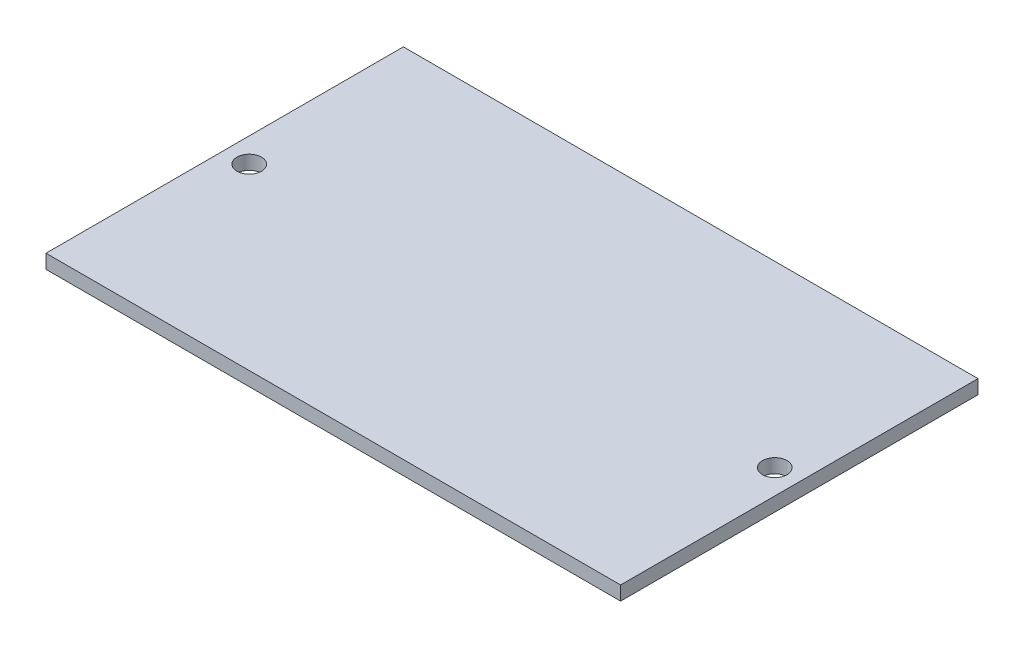
SolidWorks part; units mm, degrees
ref_plane "Front Plane" through (0, 0, 0) normal (0, 0, 1) x (1, 0, 0)
ref_plane "Top Plane" through (0, 0, 0) normal (0, 1, 0) x (1, 0, 0)
ref_plane "Right Plane" through (0, 0, 0) normal (1, 0, 0) x (0, 0, -1)
sketch "Sketch1" plane through (0, 0, 0) normal (0, 1, 0) x (1, 0, 0)
  line L1 (0, 0) -> (82, 0)
  line L2 (0, 0) -> (0, 51)
  line L3 (0, 51) -> (82, 51)
  line L4 (82, 0) -> (82, 51)
  dimension "D1" = 82
  dimension "D2" = 51
extrude "Boss-Extrude1" add sketch "Sketch1" along normal blind 2
sketch "Sketch2" plane through (0, 2, 0) normal (0, 1, 0) x (1, 0, 0)
  line L0 (3.5, 25.5) -> (78.5, 25.5) construction
  line L1 (41, 25.5) -> (41, 0) construction
  line L2 (0, 0) -> (82, 0) construction
  line L3 (78.5, 25.5) -> (82, 25.5) construction
  line L4 (82, 0) -> (82, 51) construction
  circle A0 centre (3.5, 25.5) radius 1.75
  circle A1 centre (78.5, 25.5) radius 1.75
  dimension "D2" = 3.5
  dimension "D1" = 75
extrude "Cut-Extrude1" cut sketch "Sketch2" against normal blind 2
